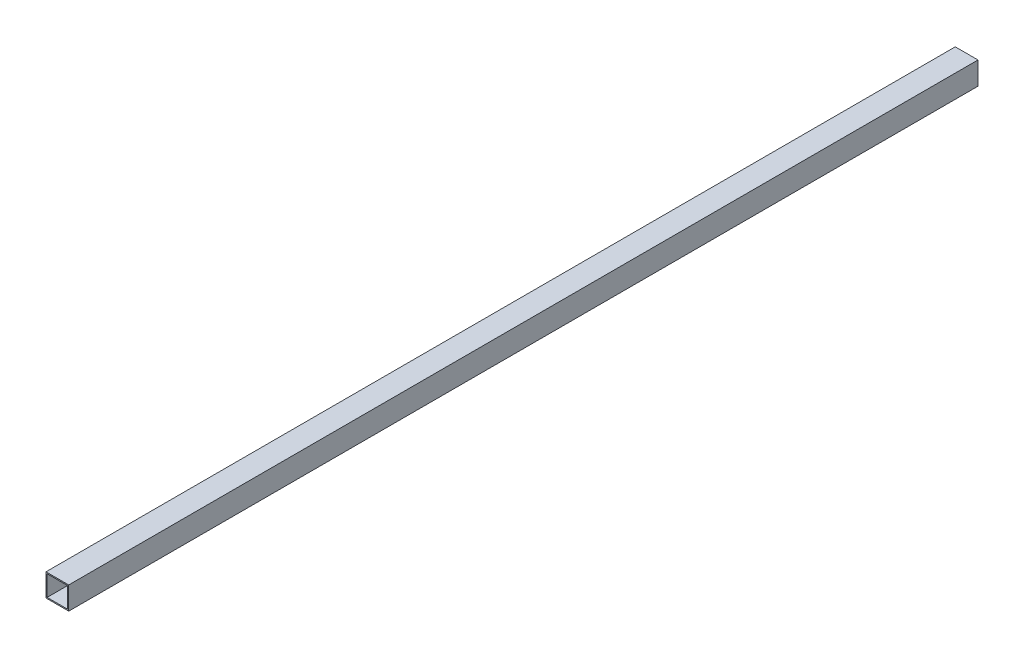
SolidWorks part; units mm, degrees
ref_plane "Спереди" through (0, 0, 0) normal (0, 0, 1) x (1, 0, 0)
ref_plane "Сверху" through (0, 0, 0) normal (0, 1, 0) x (1, 0, 0)
ref_plane "Справа" through (0, 0, 0) normal (1, 0, 0) x (0, 0, -1)
sketch "Эскиз1" plane through (0, 0, 0) normal (0, 0, 1) x (1, 0, 0)
  line L1 (4.5, -4.5) -> (-4.5, -4.5)
  line L2 (4.5, -4.5) -> (4.5, 4.5)
  line L3 (4.5, 4.5) -> (-4.5, 4.5)
  line L4 (-4.5, -4.5) -> (-4.5, 4.5)
  line L5 (4.5, -4.5) -> (-4.5, 4.5) construction
  line L6 (4.5, 4.5) -> (-4.5, -4.5) construction
  line L7 (5, -5) -> (-5, -5)
  line L8 (5, -5) -> (5, 5)
  line L9 (5, 5) -> (-5, 5)
  line L10 (-5, -5) -> (-5, 5)
  line L11 (5, -5) -> (-5, 5) construction
  line L12 (5, 5) -> (-5, -5) construction
  point P0 (0, 0)
  point P6 (0, 0)
  dimension "D1" = 9
  dimension "D2" = 9
  dimension "D3" = 10
  dimension "D4" = 10
extrude "Бобышка-Вытянуть1" add sketch "Эскиз1" along normal blind 400
